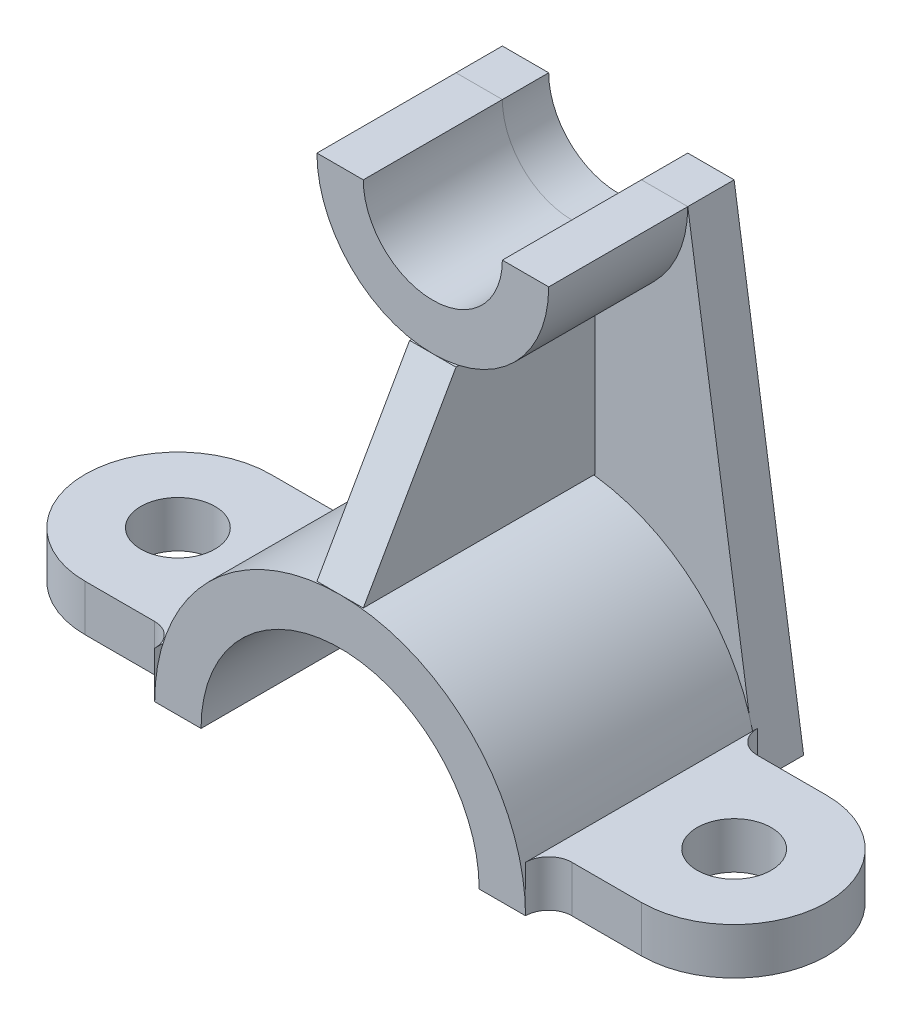
SolidWorks part; units mm, degrees
ref_plane "Front Plane" through (0, 0, 0) normal (0, 0, 1) x (1, 0, 0)
ref_plane "Top Plane" through (0, 0, 0) normal (0, 1, 0) x (1, 0, 0)
ref_plane "Right Plane" through (0, 0, 0) normal (1, 0, 0) x (0, 0, -1)
sketch "Sketch1" plane through (0, 0, 0) normal (0, 0, 1) x (1, 0, 0)
  line L0 (-149.1907, 0) -> (184.8538, 0) construction
  line L1 (-40, 0) -> (-30, 0)
  line L2 (30, 0) -> (40, 0)
  arc A0 (40, 0) -> (-40, 0) centre (0, 0) ccw
  arc A1 (30, 0) -> (-30, 0) centre (0, 0) ccw
  dimension "D1" = 80
  dimension "D2" = 60
extrude "Boss-Extrude1" add sketch "Sketch1" against normal blind 50
sketch "Sketch2" plane through (0, 0, 0) normal (1, 0, 0) x (0, 0, -1)
  line L0 (0, 40) -> (20, 75)
  line L1 (20, 75) -> (50, 75)
  line L2 (50, 75) -> (50, 40)
  line L3 (50, 40) -> (0, 40)
  dimension "D1" = 35
  dimension "D2" = 30
extrude "Boss-Extrude2" add sketch "Sketch2" along normal mid plane 10 separate body
ref_plane "Plane1" through (0, 0, -20) normal (0, 0, -1) x (-1, 0, 0)
sketch "Sketch4" plane through (0, 0, -20) normal (0, 0, -1) x (-1, 0, 0)
  line L0 (0, 0) -> (0, 100) construction
  line L1 (-5, 75) -> (5, 75) construction
  line L2 (-25, 100) -> (-15, 100)
  line L3 (15, 100) -> (42.9107, 100)
  arc A0 (-25, 100) -> (25, 100) centre (0, 100) ccw
  arc A1 (-15, 100) -> (15, 100) centre (0, 100) ccw
  dimension "D1" = 30
  dimension "D2" = 50
  dimension "D3" = 25
extrude "Boss-Extrude3" add sketch "Sketch4" along normal blind 30 separate body contours L0 A0 L3 A1 | A0 L0 A1 L2
ref_plane "Plane2" through (0, 0, -50) normal (0, 0, 1) x (1, 0, 0)
sketch "Sketch5" plane through (0, 0, -50) normal (0, 0, 1) x (1, 0, 0)
  line L0 (-25, 100) -> (-40, 0)
  line L1 (25, 100) -> (40, 0)
  line L2 (-25, 100) -> (-15, 100)
  line L3 (-15, 100) -> (-14.8026, 99.6876)
  line L4 (15, 100) -> (25, 100)
  line L6 (40, 0) -> (30, 0)
  line L7 (-30, 0) -> (-40, 0)
  arc A0 (30, 0) -> (-30, 0) centre (0, 0) ccw
  arc A1 (-25, 100) -> (25, 100) centre (0, 100) ccw
  arc A2 (-15, 100) -> (15, 100) centre (0, 100) ccw
  arc A3 (-15, 100) -> (15, 100) centre (0, 100) ccw construction
  arc A4 (40, 0) -> (-40, 0) centre (0, 0) ccw
  dimension "D1" = 10
extrude "Boss-Extrude5" add sketch "Sketch5" against normal blind 10 separate body contours A4 L1 A1 L0 | A2 L2 A1 L4 | L1 A4 L0 L7 A0 L6
sketch "Sketch6" plane through (0, 0, 0) normal (0, 1, 0) x (1, 0, 0)
  line L0 (40, 50) -> (40, 0) construction
  line L1 (40, 5) -> (60, 5)
  line L2 (40, 5) -> (40, 45)
  line L3 (40, 45) -> (60, 45)
  line L4 (60, 5) -> (60, 17)
  line L5 (40, 0) -> (45, 0)
  line L6 (60, 25) -> (38.1556, 25) construction
  line L7 (40, 45) -> (40, 50)
  line L8 (40, 5) -> (40, 0)
  line L9 (40, 50) -> (40, 45)
  arc A0 (60, 5) -> (60, 45) centre (60, 25) ccw
  circle A1 centre (60, 25) radius 8
  arc A2 (40, 0) -> (45, 5) centre (45, 0) cw
  arc A3 (40, 50) -> (45, 45) centre (45, 50) ccw
  dimension "D4" = 16
  dimension "D1" = 20
  dimension "D2" = 40
  dimension "D3" = 5
  dimension "D5" = 25
  dimension "D6" = 5
extrude "Boss-Extrude9" add sketch "Sketch6" along normal blind 10 contours A3 L7 L3 | L6 A1 L4 A0 L3 L2 | A1 L6 L2 L1 L4 | L8 A2 L1
mirror "Mirror3" about plane through (0, 0, 0) normal (1, 0, 0)
